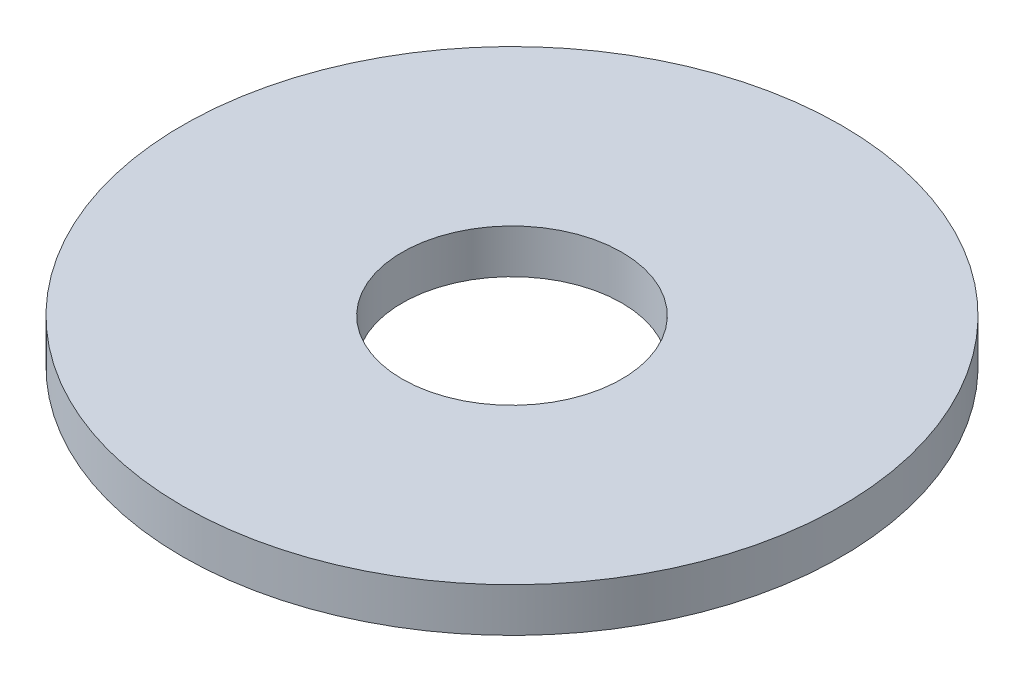
SolidWorks part; units mm, degrees
ref_plane "Front Plane" through (0, 0, 0) normal (0, 0, 1) x (1, 0, 0)
ref_plane "Top Plane" through (0, 0, 0) normal (0, 1, 0) x (1, 0, 0)
ref_plane "Right Plane" through (0, 0, 0) normal (1, 0, 0) x (0, 0, -1)
sketch "Sketch1" plane through (0, 0, 0) normal (0, 1, 0) x (1, 0, 0)
  circle A0 centre (0, 0) radius 30
  dimension "D1" = 60
extrude "Boss-Extrude1" add sketch "Sketch1" along normal blind 4
sketch "Sketch2" plane through (0, 4, 0) normal (0, 1, 0) x (1, 0, 0)
  circle A0 centre (0, 0) radius 10
  dimension "D1" = 20
extrude "Cut-Extrude1" cut sketch "Sketch2" against normal blind 10
sketch "Croquis1" plane through (0, 4, 0) normal (0, 1, 0) x (1, 0, 0)
  line L0 (0, 0) -> (0, 30) construction
  circle A0 centre (0, 0) radius 30 construction
